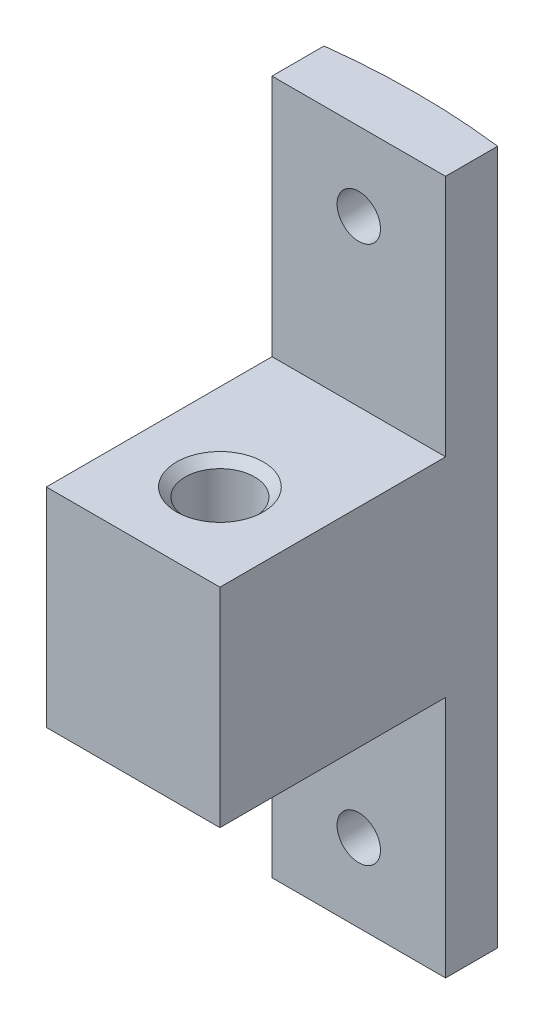
SolidWorks part; units mm, degrees
material "Alliage 1060"
ref_plane "Plan de face" through (0, 0, 0) normal (0, 0, 1) x (1, 0, 0)
ref_plane "Plan de dessus" through (0, 0, 0) normal (0, 1, 0) x (1, 0, 0)
ref_plane "Plan de droite" through (0, 0, 0) normal (1, 0, 0) x (0, 0, -1)
sketch "Esquisse1" plane through (0, 0, 0) normal (0, 1, 0) x (1, 0, 0)
  line L0 (0, 0) -> (10, 0)
  line L1 (10, 0) -> (10, 3)
  line L2 (0, 3) -> (0, 0)
  line L3 (5, 0) -> (5, -74.8163) construction
  arc A0 (0, 3) -> (10, 3) centre (5, -37.694) cw
  dimension "D4" = 41
  dimension "D1" = 10
  dimension "D2" = 3
extrude "Boss.-Extru.1" add sketch "Esquisse1" along normal blind 20
sketch "Esquisse2" plane through (0, 0, 0) normal (0, -1, 0) x (1, 0, 0)
  line L1 (10, 0) -> (0, 0)
  line L2 (10, 0) -> (10, 13)
  line L3 (10, 13) -> (0, 13)
  line L4 (0, 0) -> (0, 13)
  dimension "D1" = 13
  dimension "D2" = 10
extrude "Boss.-Extru.2" add sketch "Esquisse2" against normal blind 6
hole_wizard "Dégagement M41" positions "Esquisse3" profile "Esquisse4" hole size "M4" standard "ISO" end condition through all
sketch "Esquisse3" plane through (0, 6, 0) normal (0, 1, 0) x (1, 0, 0)
  line L0 (0, -13) -> (0, 0) construction
  line L1 (10, -13) -> (0, -13) construction
  point P0 (5, -8)
  dimension "D1" = 5
  dimension "D2" = 5
sketch "Esquisse4" plane through (5, 6, 8) normal (1, 0, 0) x (0, 0, 1)
  line L0 (0, 0) -> (0, 26)
  line L1 (0, 26) -> (2, 26)
  line L2 (2, 26) -> (2, 0.5)
  line L3 (2, 0.5) -> (2.5, 0)
  line L5 (2.5, 0) -> (0, 0)
  line L6 (-2, 0.5) -> (-2.5, 0) construction
  line L11 (0, -6.35) -> (0, 107.95) construction
  dimension "Diamètre du perçage jusqu'au prochain" = 4
  dimension "Profondeur du perçage jusqu'au prochain" = 26
  dimension "Diamètre du fraisage entrant" = 5
  dimension "Angle du fraisage entrant" = 90
hole_wizard "Dégagement M2.51" positions "Esquisse3D1" profile "Esquisse5" hole size "M2.5" standard "ISO" end condition through all
sketch3d "Esquisse3D1"
  point P0 (5, 15.5, -3.306)
  dimension "D1" = 5
  dimension "D2" = 4.5
sketch "Esquisse5" plane through (5, 15.5, -3.306) normal (1, 0, 0) x (0, 1, 0)
  line L0 (0, 0) -> (0, 16.306)
  line L1 (0, 16.306) -> (1.25, 16.306)
  line L2 (1.25, 16.306) -> (1.25, 0)
  line L5 (1.25, 0) -> (0, 0)
  line L11 (0, -6.35) -> (0, 107.95) construction
  dimension "Diamètre du perçage jusqu'au prochain" = 2.5
  dimension "Profondeur du perçage jusqu'au prochain" = 16.306
mirror "Symétrie1" about plane through (5, 0, 37.694) normal (0, -1, 0) of "Dégagement M41", "Boss.-Extru.2", "Boss.-Extru.1", "Dégagement M2.51"
